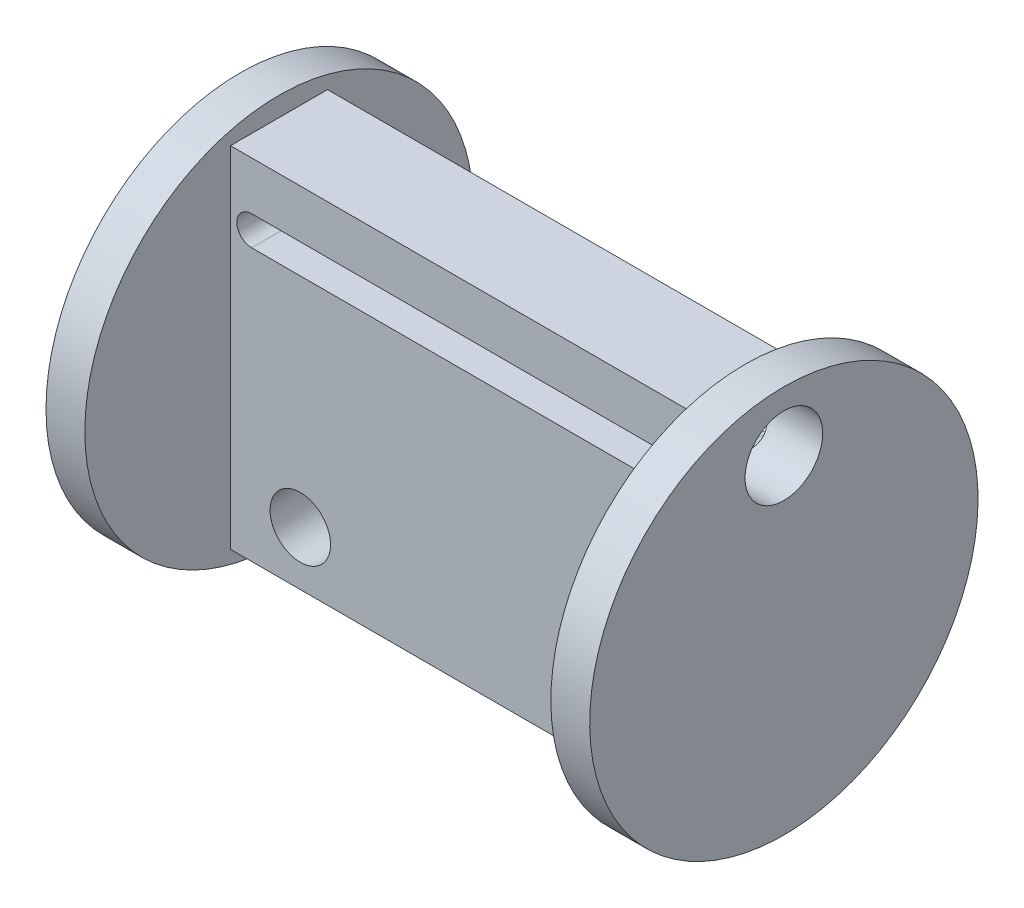
SolidWorks part; units mm, degrees
ref_plane "Front Plane" through (0, 0, 0) normal (0, 0, 1) x (1, 0, 0)
ref_plane "Top Plane" through (0, 0, 0) normal (0, 1, 0) x (1, 0, 0)
ref_plane "Right Plane" through (0, 0, 0) normal (1, 0, 0) x (0, 0, -1)
sketch "Sketch1" plane through (0, 0, 0) normal (0, 0, 1) x (1, 0, 0)
  line L1 (0, 0) -> (24, 0)
  line L2 (0, 0) -> (0, -18)
  line L3 (0, -18) -> (24, -18)
  line L4 (24, 0) -> (24, -18)
  dimension "D1" = 18
  dimension "D2" = 24
extrude "Boss-Extrude1" add sketch "Sketch1" along normal blind 5
sketch "Sketch3" plane through (0, 0, 5) normal (0, 0, 1) x (1, 0, 0)
  line L0 (3.5959, -15.225) -> (3.5959, -18) construction
  line L1 (0, -18) -> (24, -18) construction
  line L2 (3.5959, -15.225) -> (0, -15.225) construction
  line L3 (0, 0) -> (0, -18) construction
  line L4 (12, 0) -> (12, -18) construction
  line L5 (24, 0) -> (0, 0) construction
  line L6 (2.0384, -15.225) -> (20.7074, -15.225) construction
  circle A0 centre (3.5959, -15.225) radius 1.5575
  circle A2 centre (19.1499, -15.225) radius 1.5575
  dimension "D1" = 2.775
  dimension "D4" = 3.115
  dimension "D2" = 3.5959
  dimension "D3" = 18.669
extrude "Cut-Extrude1" cut sketch "Sketch3" against normal through all
sketch "Sketch4" plane through (0, 0, 5) normal (0, 0, 1) x (1, 0, 0)
  line L0 (12, 0) -> (12, -3.25) construction
  line L1 (24, 0) -> (0, 0) construction
  line L2 (1.0895, -3.25) -> (22.6087, -3.25) construction
  line L3 (1.0895, -2.49) -> (22.6087, -2.49)
  line L4 (1.0895, -4.01) -> (22.6087, -4.01)
  arc A0 (1.0895, -2.49) -> (1.0895, -4.01) centre (1.0895, -3.25) ccw
  arc A1 (22.6087, -4.01) -> (22.6087, -2.49) centre (22.6087, -3.25) ccw
  point P6 (11.8491, -3.25)
  point P11 (22.6087, -2.4344)
  dimension "D1" = 3.25
extrude "Cut-Extrude2" cut sketch "Sketch4" against normal through all
sketch "Sketch5" plane through (0, 0, 0) normal (-1, 0, 0) x (0, 0, 1)
  line L0 (2.5, 0) -> (2.5, -18) construction
  line L1 (5, 0) -> (0, 0) construction
  line L2 (5, -18) -> (0, -18) construction
  circle A1 centre (2.5, -9) radius 10
  point P9 (-15.9589, -10.1041)
extrude "Boss-Extrude3" add sketch "Sketch5" along normal blind 2
sketch "Sketch6" plane through (24, 0, 0) normal (1, 0, 0) x (0, 0, -1)
  line L0 (-2.5, 0) -> (-2.5, -18) construction
  line L1 (-5, 0) -> (0, 0) construction
  line L2 (-5, -18) -> (0, -18) construction
  circle A1 centre (-2.5, -9) radius 10
extrude "Boss-Extrude4" add sketch "Sketch6" along normal blind 2
sketch "Sketch7" plane through (26, 0, 0) normal (1, 0, 0) x (0, 0, -1)
  line L0 (-2.5, 1) -> (-2.5, -2.0762) construction
  circle A0 centre (-2.5, -9) radius 10 construction
  circle A1 centre (-2.5, -2.0762) radius 2
  dimension "D1" = 3.0762
extrude "Cut-Extrude3" cut sketch "Sketch7" against normal through all
